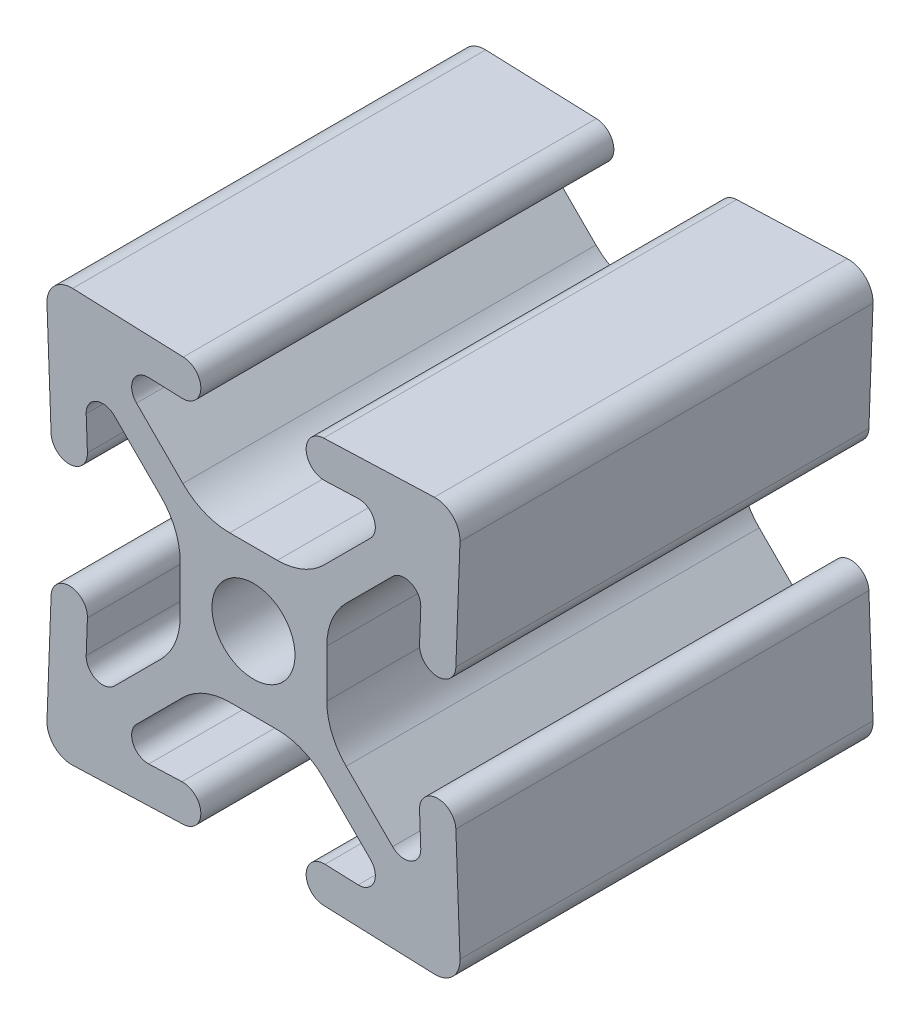
SolidWorks part; units mm, degrees
material "6061 Alloy"
ref_plane "Front" through (0, 0, 0) normal (0, 0, 1) x (1, 0, 0)
ref_plane "Top" through (0, 0, 0) normal (0, 1, 0) x (1, 0, 0)
ref_plane "Right" through (0, 0, 0) normal (1, 0, 0) x (0, 0, -1)
sketch "Sketch1" plane through (0, 0, 0) normal (0, 0, 1) x (1, 0, 0)
  line L0 (11.1192, 12.6989) -> (4.3145, 12.4452)
  line L1 (6.4391, 10.2877) -> (4.3977, 10.2116)
  line L2 (12.6989, 11.1192) -> (12.4452, 4.3145)
  line L3 (7.1954, 8.554) -> (4.3403, 5.6988)
  line L4 (10.2877, 6.4391) -> (10.2116, 4.3977)
  line L5 (0, 4.5085) -> (1.4666, 4.5085)
  line L6 (0, 4.5085) -> (-1.4666, 4.5085)
  line L7 (8.554, 7.1954) -> (5.6988, 4.3403)
  line L8 (-7.1954, 8.554) -> (-4.3403, 5.6988)
  line L9 (4.5085, 0) -> (4.5085, 1.4666)
  line L10 (4.5085, 0) -> (4.5085, -1.4666)
  line L11 (-6.4391, 10.2877) -> (-4.3977, 10.2116)
  line L12 (8.554, -7.1954) -> (5.6988, -4.3403)
  line L13 (-11.1192, 12.6989) -> (-4.3145, 12.4452)
  line L14 (10.2877, -6.4391) -> (10.2116, -4.3977)
  line L15 (-12.6989, 11.1192) -> (-12.4452, 4.3145)
  line L16 (12.6989, -11.1192) -> (12.4452, -4.3145)
  line L17 (-10.2877, 6.4391) -> (-10.2116, 4.3977)
  line L18 (11.1192, -12.6989) -> (4.3145, -12.4452)
  line L19 (-8.554, 7.1954) -> (-5.6988, 4.3403)
  line L20 (6.4391, -10.2877) -> (4.3977, -10.2116)
  line L21 (-4.5085, 0) -> (-4.5085, 1.4666)
  line L22 (-4.5085, 0) -> (-4.5085, -1.4666)
  line L23 (7.1954, -8.554) -> (4.3403, -5.6988)
  line L24 (-8.554, -7.1954) -> (-5.6988, -4.3403)
  line L25 (0, -4.5085) -> (1.4666, -4.5085)
  line L26 (0, -4.5085) -> (-1.4666, -4.5085)
  line L27 (-10.2877, -6.4391) -> (-10.2116, -4.3977)
  line L28 (-7.1954, -8.554) -> (-4.3403, -5.6988)
  line L29 (-12.6989, -11.1192) -> (-12.4452, -4.3145)
  line L30 (-6.4391, -10.2877) -> (-4.3977, -10.2116)
  line L31 (-11.1192, -12.6989) -> (-4.3145, -12.4452)
  arc A0 (4.3145, 12.4452) -> (4.3977, 10.2116) centre (4.3561, 11.3284) ccw
  arc A1 (12.2536, 12.2536) -> (11.1192, 12.6989) centre (11.176, 11.176) ccw
  arc A2 (12.6989, 11.1192) -> (12.2536, 12.2536) centre (11.176, 11.176) ccw
  arc A3 (7.1954, 8.554) -> (6.4391, 10.2877) centre (6.477, 9.2724) ccw
  arc A4 (10.2116, 4.3977) -> (12.4452, 4.3145) centre (11.3284, 4.3561) ccw
  arc A5 (1.4666, 4.5085) -> (4.3403, 5.6988) centre (1.4666, 8.5725) ccw
  arc A6 (10.2877, 6.4391) -> (8.554, 7.1954) centre (9.2724, 6.477) ccw
  arc A7 (-4.3403, 5.6988) -> (-1.4666, 4.5085) centre (-1.4666, 8.5725) ccw
  arc A8 (5.6988, 4.3403) -> (4.5085, 1.4666) centre (8.5725, 1.4666) ccw
  arc A9 (-6.4391, 10.2877) -> (-7.1954, 8.554) centre (-6.477, 9.2724) ccw
  arc A10 (4.5085, -1.4666) -> (5.6988, -4.3403) centre (8.5725, -1.4666) ccw
  arc A11 (-4.3977, 10.2116) -> (-4.3145, 12.4452) centre (-4.3561, 11.3284) ccw
  arc A12 (8.554, -7.1954) -> (10.2877, -6.4391) centre (9.2724, -6.477) ccw
  arc A13 (-11.1192, 12.6989) -> (-12.2536, 12.2536) centre (-11.176, 11.176) ccw
  arc A14 (-12.2536, 12.2536) -> (-12.6989, 11.1192) centre (-11.176, 11.176) ccw
  arc A15 (12.4452, -4.3145) -> (10.2116, -4.3977) centre (11.3284, -4.3561) ccw
  arc A16 (-12.4452, 4.3145) -> (-10.2116, 4.3977) centre (-11.3284, 4.3561) ccw
  arc A17 (12.2536, -12.2536) -> (12.6989, -11.1192) centre (11.176, -11.176) ccw
  arc A18 (11.1192, -12.6989) -> (12.2536, -12.2536) centre (11.176, -11.176) ccw
  arc A19 (-8.554, 7.1954) -> (-10.2877, 6.4391) centre (-9.2724, 6.477) ccw
  arc A20 (4.3977, -10.2116) -> (4.3145, -12.4452) centre (4.3561, -11.3284) ccw
  arc A21 (-4.5085, 1.4666) -> (-5.6988, 4.3403) centre (-8.5725, 1.4666) ccw
  arc A22 (6.4391, -10.2877) -> (7.1954, -8.554) centre (6.477, -9.2724) ccw
  arc A23 (-5.6988, -4.3403) -> (-4.5085, -1.4666) centre (-8.5725, -1.4666) ccw
  arc A24 (4.3403, -5.6988) -> (1.4666, -4.5085) centre (1.4666, -8.5725) ccw
  arc A25 (-10.2877, -6.4391) -> (-8.554, -7.1954) centre (-9.2724, -6.477) ccw
  arc A26 (-1.4666, -4.5085) -> (-4.3403, -5.6988) centre (-1.4666, -8.5725) ccw
  arc A27 (-10.2116, -4.3977) -> (-12.4452, -4.3145) centre (-11.3284, -4.3561) ccw
  arc A28 (-7.1954, -8.554) -> (-6.4391, -10.2877) centre (-6.477, -9.2724) ccw
  arc A29 (-12.6989, -11.1192) -> (-12.2536, -12.2536) centre (-11.176, -11.176) ccw
  arc A30 (-12.2536, -12.2536) -> (-11.1192, -12.6989) centre (-11.176, -11.176) ccw
  arc A31 (-4.3145, -12.4452) -> (-4.3977, -10.2116) centre (-4.3561, -11.3284) ccw
  arc A32 (1.805, 1.805) -> (0, 2.5527) centre (0, 0) ccw
  arc A33 (0, 2.5527) -> (-1.805, 1.805) centre (0, 0) ccw
  arc A34 (2.5527, 0) -> (1.805, 1.805) centre (0, 0) ccw
  arc A35 (-1.805, 1.805) -> (-2.5527, 0) centre (0, 0) ccw
  arc A36 (1.805, -1.805) -> (2.5527, 0) centre (0, 0) ccw
  arc A37 (-2.5527, 0) -> (-1.805, -1.805) centre (0, 0) ccw
  arc A38 (0, -2.5527) -> (1.805, -1.805) centre (0, 0) ccw
  arc A39 (-1.805, -1.805) -> (0, -2.5527) centre (0, 0) ccw
extrude "Extrude1" add sketch "Sketch1" along normal blind 25.4
